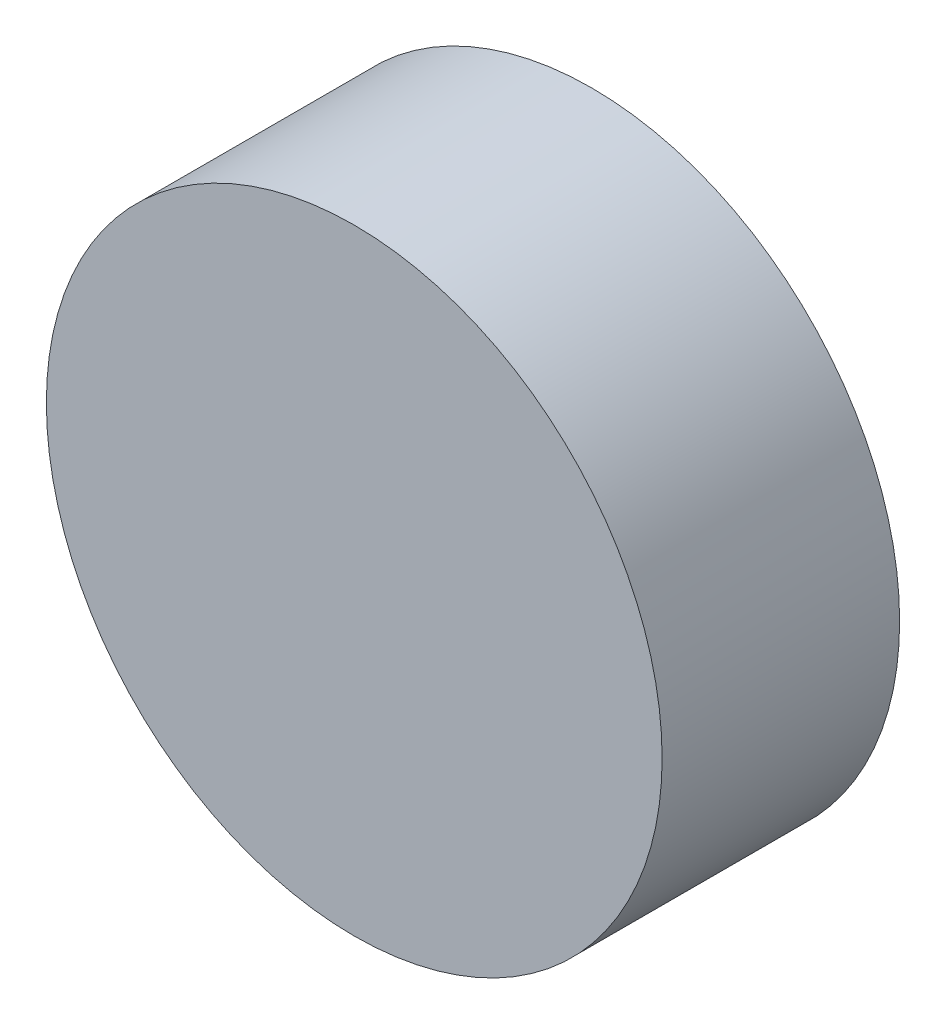
SolidWorks part; units mm, degrees
ref_plane "Front Plane" through (0, 0, 0) normal (0, 0, 1) x (1, 0, 0)
ref_plane "Top Plane" through (0, 0, 0) normal (0, 1, 0) x (1, 0, 0)
ref_plane "Right Plane" through (0, 0, 0) normal (1, 0, 0) x (0, 0, -1)
sketch "Sketch1" plane through (0, 0, 0) normal (0, 0, 1) x (1, 0, 0)
  circle A0 centre (0, 0) radius 35
  dimension "D1" = 70
extrude "Boss-Extrude1" add sketch "Sketch1" along normal mid plane 27
ref_plane "Plane1" through (0, 0, 0) normal (0, 0, -1) x (-1, 0, 0)
